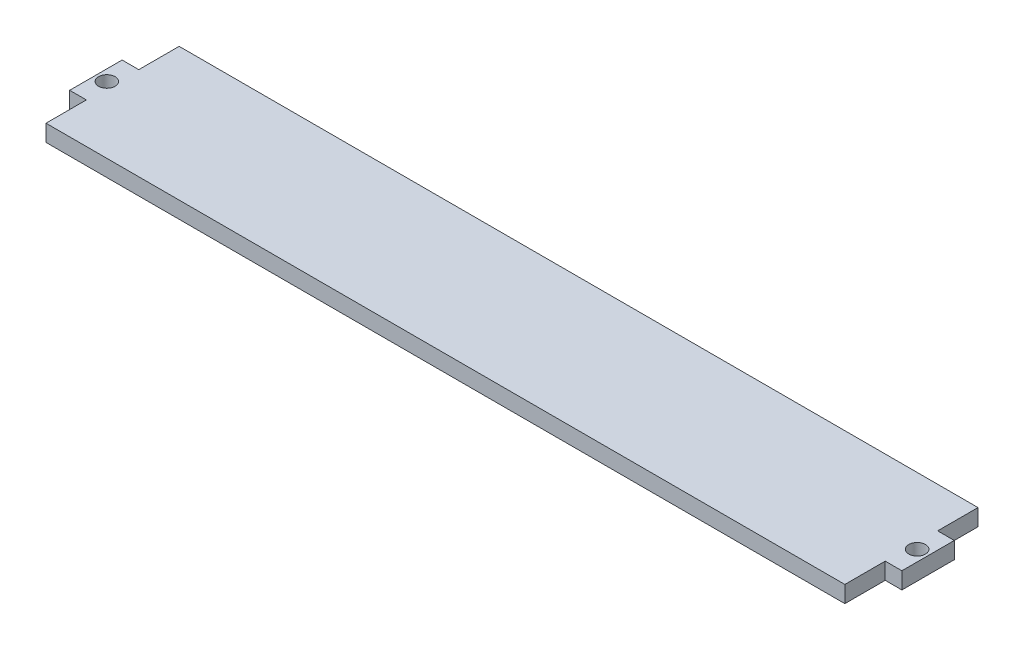
SolidWorks part; units mm, degrees
ref_plane "Front Plane" through (0, 0, 0) normal (0, 0, 1) x (1, 0, 0)
ref_plane "Top Plane" through (0, 0, 0) normal (0, 1, 0) x (1, 0, 0)
ref_plane "Right Plane" through (0, 0, 0) normal (1, 0, 0) x (0, 0, -1)
sketch "Sketch2" plane through (0, 0, 0) normal (0, 1, 0) x (1, 0, 0)
  line L1 (76.2, 12.7) -> (-76.2, 12.7)
  line L2 (76.2, 12.7) -> (76.2, -12.7)
  line L3 (76.2, -12.7) -> (-76.2, -12.7)
  line L4 (-76.2, 12.7) -> (-76.2, -12.7)
  line L5 (76.2, 12.7) -> (-76.2, -12.7) construction
  line L6 (76.2, -12.7) -> (-76.2, 12.7) construction
  point P0 (0, 0)
  dimension "D1" = 152.4
  dimension "D2" = 25.4
extrude "Boss-Extrude1" add sketch "Sketch2" along normal blind 3.18
sketch "Sketch3" plane through (-76.2, 0, 0) normal (-1, 0, 0) x (0, 0, 1)
  line L0 (0, 0) -> (0, 3.18) construction
  line L1 (-12.7, 0) -> (12.7, 0) construction
  line L2 (-12.7, 3.18) -> (12.7, 3.18) construction
  line L4 (-5, 3.18) -> (5, 3.18)
  line L5 (-5, 3.18) -> (-5, 0)
  line L6 (-5, 0) -> (5, 0)
  line L7 (5, 3.18) -> (5, 0)
  line L8 (-5, 3.18) -> (5, 0) construction
  line L9 (-5, 0) -> (5, 3.18) construction
  point P6 (0, 1.59)
  dimension "D1" = 10
extrude "Boss-Extrude2" add sketch "Sketch3" along normal blind 3.18 contours L5 L6 L7 L4
sketch "Sketch4" plane through (76.2, 0, 0) normal (1, 0, 0) x (0, 0, -1)
  line L0 (0, 0) -> (0, 3.18) construction
  line L1 (-12.7, 0) -> (12.7, 0) construction
  line L2 (-12.7, 3.18) -> (12.7, 3.18) construction
  line L4 (-5, 3.18) -> (5, 3.18)
  line L5 (-5, 3.18) -> (-5, 0)
  line L6 (-5, 0) -> (5, 0)
  line L7 (5, 3.18) -> (5, 0)
  line L8 (-5, 3.18) -> (5, 0) construction
  line L9 (-5, 0) -> (5, 3.18) construction
  point P6 (0, 1.59)
  dimension "D1" = 10
extrude "Boss-Extrude3" add sketch "Sketch4" along normal blind 3.18
sketch "Sketch5" plane through (0, 3.18, 0) normal (0, 1, 0) x (1, 0, 0)
  line L0 (78.88, 0) -> (79.38, 0) construction
  line L1 (79.38, 5) -> (79.38, -5) construction
  line L2 (0, -12.7) -> (0, 12.7) construction
  line L3 (-76.2, -12.7) -> (76.2, -12.7) construction
  line L4 (76.2, 12.7) -> (-76.2, 12.7) construction
  line L5 (-78.88, 0) -> (-79.38, 0) construction
  circle A0 centre (77.29, 0) radius 1.59
  circle A1 centre (-77.29, 0) radius 1.59
  dimension "D1" = 3.18
  dimension "D2" = 0.5
extrude "Cut-Extrude1" cut sketch "Sketch5" against normal blind 3.18
